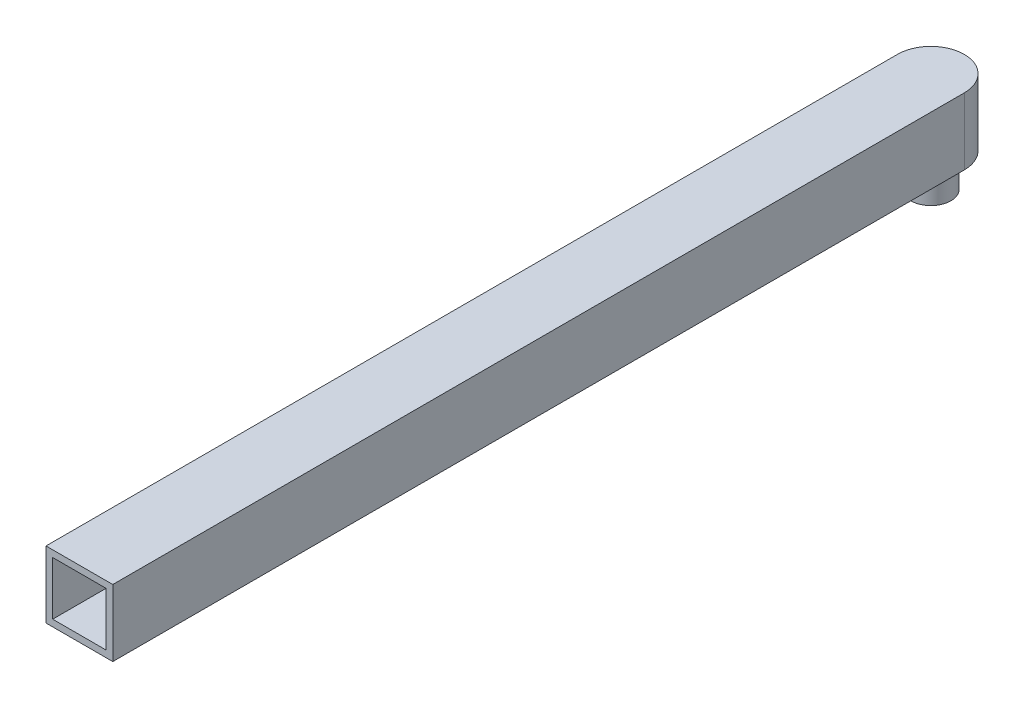
SolidWorks part; units mm, degrees
ref_plane "Front Plane" through (0, 0, 0) normal (0, 0, 1) x (1, 0, 0)
ref_plane "Top Plane" through (0, 0, 0) normal (0, 1, 0) x (1, 0, 0)
ref_plane "Right Plane" through (0, 0, 0) normal (1, 0, 0) x (0, 0, -1)
sketch "Sketch1" plane through (0, 0, 0) normal (0, 1, 0) x (1, 0, 0)
  line L1 (-12.7, -161.925) -> (12.7, -161.925)
  line L2 (-12.7, -161.925) -> (-12.7, 161.925)
  line L4 (12.7, -161.925) -> (12.7, 161.925)
  line L5 (-12.7, -161.925) -> (12.7, 161.925) construction
  line L6 (-12.7, 161.925) -> (12.7, -161.925) construction
  arc A0 (-12.7, 161.925) -> (12.7, 161.925) centre (0, 161.925) cw
  point P0 (0, 0)
  dimension "D1" = 25.4
  dimension "D2" = 323.85
extrude "Boss-Extrude1" add sketch "Sketch1" along normal blind 25.4 contours L4 A0 L2 L1
sketch "Sketch2" plane through (0, 0, 161.925) normal (0, 0, 1) x (1, 0, 0)
  line L0 (-10.16, 2.54) -> (10.16, 2.54)
  line L1 (10.16, 2.54) -> (10.16, 22.86)
  line L2 (10.16, 22.86) -> (-10.16, 22.86)
  line L3 (-10.16, 22.86) -> (-10.16, 2.54)
  line L4 (-12.7, 0) -> (12.7, 0)
  line L5 (12.7, 0) -> (12.7, 25.4)
  line L6 (12.7, 25.4) -> (-12.7, 25.4)
  line L7 (-12.7, 25.4) -> (-12.7, 0)
  line L8 (-12.7, 0) -> (12.7, 0)
  line L9 (12.7, 0) -> (12.7, 25.4)
  line L10 (12.7, 25.4) -> (-12.7, 25.4)
  line L11 (-12.7, 25.4) -> (-12.7, 0)
  dimension "D1" = 0
  dimension "D2" = 2.54
extrude "Cut-Extrude1" cut sketch "Sketch2" against normal blind 322.58 contours L0 L1 L2 L3
sketch "Sketch3" plane through (0, 0, 0) normal (0, -1, 0) x (1, 0, 0)
  circle A0 centre (0, -161.925) radius 7.62
extrude "Boss-Extrude2" add sketch "Sketch3" along normal blind 12.7
